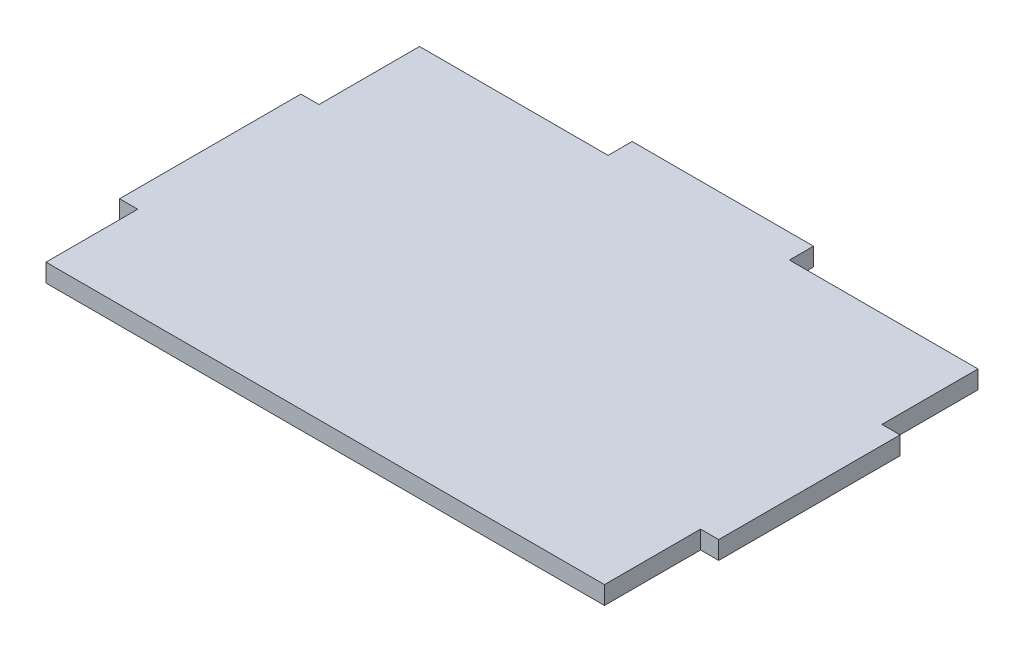
SolidWorks part; units mm, degrees
ref_plane "Front Plane" through (0, 0, 0) normal (0, 0, 1) x (1, 0, 0)
ref_plane "Top Plane" through (0, 0, 0) normal (0, 1, 0) x (1, 0, 0)
ref_plane "Right Plane" through (0, 0, 0) normal (1, 0, 0) x (0, 0, -1)
sketch "Esquisse1" plane through (0, 0, 0) normal (0, 1, 0) x (1, 0, 0)
  line L0 (77, -51.5) -> (77, -25)
  line L1 (-77, -51.5) -> (77, -51.5)
  line L5 (-77, -51.5) -> (77, 51.5) construction
  line L6 (-77, 51.5) -> (77, -51.5) construction
  line L7 (77, -25) -> (82, -25)
  line L9 (77, 25) -> (82, 25)
  line L10 (82, -25) -> (82, 25)
  line L12 (25, 51.5) -> (25, 58.1297)
  line L13 (25, 58.1297) -> (-25, 58.1297)
  line L14 (-25, 51.5) -> (-25, 58.1297)
  line L15 (-77, -26.2181) -> (-82, -26.2181)
  line L17 (-77, 23.7819) -> (-82, 23.7819)
  line L18 (-82, -26.2181) -> (-82, 23.7819)
  line L20 (77, 25) -> (77, 51.5)
  line L21 (-77, -51.5) -> (-77, -26.2181)
  line L23 (-77, 23.7819) -> (-77, 51.5)
  line L24 (25, 51.5) -> (77, 51.5)
  line L25 (-25, 51.5) -> (-77, 51.5)
  point P0 (0, 0)
  dimension "D1" = 103
  dimension "D2" = 154
  dimension "D3" = 5
  dimension "D4" = 50
  dimension "D5" = 5
  dimension "D6" = 50
extrude "Boss.-Extru.1" add sketch "Esquisse1" along normal blind 5
